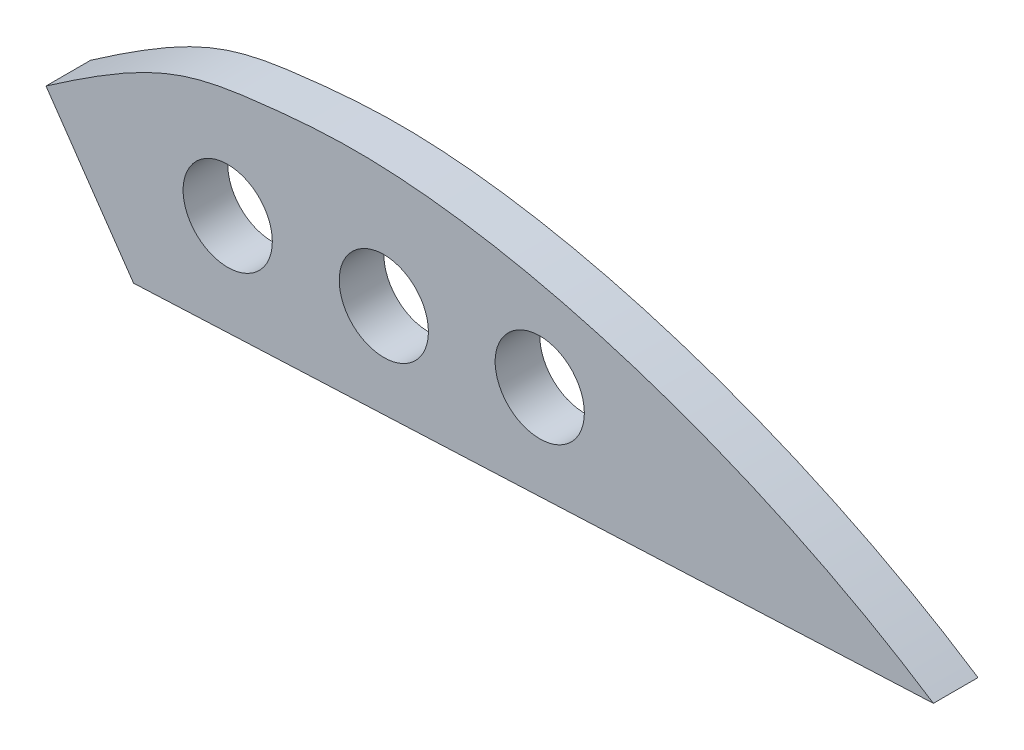
SolidWorks part; units mm, degrees
ref_plane "Front Plane" through (0, 0, 0) normal (0, 0, 1) x (1, 0, 0)
ref_plane "Top Plane" through (0, 0, 0) normal (0, 1, 0) x (1, 0, 0)
ref_plane "Right Plane" through (0, 0, 0) normal (1, 0, 0) x (0, 0, -1)
sketch "Sketch1" plane through (0, 0, 0) normal (0, 0, 1) x (1, 0, 0)
  line L0 (-169.0031, 11.7142) -> (-694.187, 895.1707) construction
  line L1 (-1743.608, 593.8305) -> (-1544.65, 573.4414) construction
  line L2 (-1743.608, 593.8305) -> (-1723.9756, 565.3542)
  line L3 (-1723.9756, 565.3542) -> (-1544.65, 573.4414)
  line L4 (-1702.8657, 588.9864) -> (-1667.8657, 588.9864) construction
  line L5 (-1667.8657, 588.9864) -> (-1632.9063, 590.6708) construction
  circle A0 centre (-1632.9063, 590.6708) radius 10
  circle A1 centre (-1667.8657, 588.9864) radius 10
  circle A2 centre (-1702.8657, 588.9864) radius 10
  spline S0 degree 3 poles (-1743.608, 593.8305) (-1719.5079, 610.5378) (-1709.3895, 613.3998) (-1646.2803, 619.2418) (-1585.7166, 600.4239) (-1544.65, 573.4414) knots 0 0 0 0 0.320555 0.420555 1 1 1 1
  dimension "D1" = 200
extrude "Boss-Extrude1" add sketch "Sketch1" along normal blind 10
